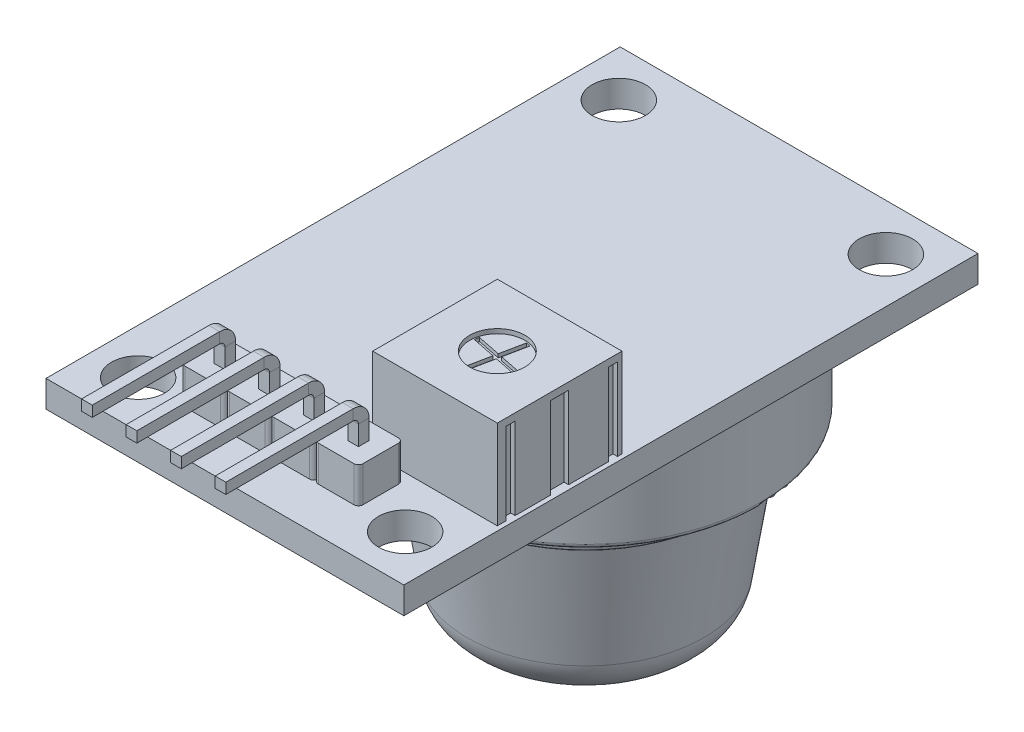
SolidWorks part; units mm, degrees
ref_plane "Front Plane" through (0, 0, 0) normal (0, 0, 1) x (1, 0, 0)
ref_plane "Top Plane" through (0, 0, 0) normal (0, 1, 0) x (1, 0, 0)
ref_plane "Right Plane" through (0, 0, 0) normal (1, 0, 0) x (0, 0, -1)
sketch "Sketch1" plane through (0, 0, 0) normal (0, 1, 0) x (1, 0, 0)
  line L1 (0, 0) -> (20.1, 0)
  line L2 (0, 0) -> (0, -32.25)
  line L3 (0, -32.25) -> (20.1, -32.25)
  line L4 (20.1, 0) -> (20.1, -32.25)
  line L5 (2.55, -2.625) -> (17.55, -2.625) construction
  line L6 (2.55, -2.625) -> (2.55, -29.625) construction
  line L7 (2.55, -29.625) -> (17.55, -29.625) construction
  line L8 (17.55, -2.625) -> (17.55, -29.625) construction
  line L9 (2.55, -2.625) -> (17.55, -29.625) construction
  line L10 (2.55, -29.625) -> (17.55, -2.625) construction
  circle A0 centre (2.55, -2.625) radius 1.5
  circle A1 centre (17.55, -2.625) radius 1.5
  circle A2 centre (2.55, -29.625) radius 1.5
  circle A3 centre (17.55, -29.625) radius 1.5
  point P5 (10.05, -16.125)
  dimension "D5" = 3
  dimension "D1" = 32.25
  dimension "D2" = 20.1
  dimension "D3" = 27
  dimension "D4" = 15
extrude "Boss-Extrude1" add sketch "Sketch1" along normal blind 1.5
sketch "Sketch2" plane through (0, 1.5, 0) normal (0, 1, 0) x (1, 0, 0)
  line L1 (5.3, -27.25) -> (7.3, -27.25)
  line L2 (5.05, -27.5) -> (5.05, -29.5)
  line L3 (5.3, -29.75) -> (7.3, -29.75)
  line L4 (6, -28.2) -> (6.6, -28.2)
  line L5 (7.8, -27.25) -> (9.8, -27.25)
  line L6 (6, -28.2) -> (6, -28.8)
  line L8 (6, -28.8) -> (6.6, -28.8)
  line L9 (7.8, -29.75) -> (9.8, -29.75)
  line L10 (6.6, -28.2) -> (6.6, -28.8)
  line L12 (9.1, -28.2) -> (9.1, -28.8)
  line L13 (8.5, -28.8) -> (9.1, -28.8)
  line L14 (6, -28.2) -> (6.6, -28.8) construction
  line L15 (8.5, -28.2) -> (8.5, -28.8)
  line L16 (8.5, -28.2) -> (9.1, -28.2)
  line L17 (0, 0) -> (0, -32.25) construction
  line L18 (0, -32.25) -> (20.1, -32.25) construction
  line L19 (10.3, -27.25) -> (12.3, -27.25)
  line L21 (10.3, -29.75) -> (12.3, -29.75)
  line L22 (6, -28.8) -> (6.6, -28.2) construction
  line L24 (11.6, -28.2) -> (11.6, -28.8)
  line L25 (11, -28.8) -> (11.6, -28.8)
  line L26 (11, -28.2) -> (11, -28.8)
  line L27 (11, -28.2) -> (11.6, -28.2)
  line L28 (12.8, -27.25) -> (14.8, -27.25)
  line L29 (15.05, -27.5) -> (15.05, -29.5)
  line L30 (12.8, -29.75) -> (14.8, -29.75)
  line L32 (14.1, -28.2) -> (14.1, -28.8)
  line L33 (13.5, -28.8) -> (14.1, -28.8)
  line L34 (13.5, -28.2) -> (13.5, -28.8)
  line L35 (13.5, -28.2) -> (14.1, -28.2)
  line L36 (7.55, -27.5) -> (7.55, -29.5) [skipped]
  line L37 (10.05, -27.5) -> (10.05, -29.5) [skipped]
  line L38 (12.55, -27.5) -> (12.55, -29.5) [skipped]
  arc A0 (7.3, -29.75) -> (7.55, -29.5) centre (7.3, -29.5) ccw
  arc A1 (5.05, -29.5) -> (5.3, -29.75) centre (5.3, -29.5) ccw
  arc A2 (5.05, -27.5) -> (5.3, -27.25) centre (5.3, -27.5) cw
  arc A3 (7.55, -27.5) -> (7.3, -27.25) centre (7.3, -27.5) ccw
  arc A4 (10.05, -27.5) -> (9.8, -27.25) centre (9.8, -27.5) ccw
  arc A5 (9.8, -29.75) -> (10.05, -29.5) centre (9.8, -29.5) ccw
  arc A6 (7.55, -29.5) -> (7.8, -29.75) centre (7.8, -29.5) ccw
  arc A7 (7.55, -27.5) -> (7.8, -27.25) centre (7.8, -27.5) cw
  arc A8 (12.55, -27.5) -> (12.3, -27.25) centre (12.3, -27.5) ccw
  arc A9 (12.3, -29.75) -> (12.55, -29.5) centre (12.3, -29.5) ccw
  arc A10 (10.05, -29.5) -> (10.3, -29.75) centre (10.3, -29.5) ccw
  arc A11 (10.05, -27.5) -> (10.3, -27.25) centre (10.3, -27.5) cw
  arc A12 (15.05, -27.5) -> (14.8, -27.25) centre (14.8, -27.5) ccw
  arc A13 (14.8, -29.75) -> (15.05, -29.5) centre (14.8, -29.5) ccw
  arc A14 (12.55, -29.5) -> (12.8, -29.75) centre (12.8, -29.5) ccw
  arc A15 (12.55, -27.5) -> (12.8, -27.25) centre (12.8, -27.5) cw
  point P8 (5.05, -29.75)
  point P11 (5.05, -27.25)
  point P14 (7.55, -27.25)
  point P23 (6.3, -28.5)
  dimension "D3" = 0.25
  dimension "D1" = 2.5
  dimension "D2" = 2.5
  dimension "D5" = 5.05
  dimension "D6" = 2.5
  dimension "D7" = 0.6
  dimension "D8" = 0.6
extrude "Boss-Extrude2" add sketch "Sketch2" along normal blind 2
sketch "Sketch3" plane through (5.05, 0, 0) normal (-1, 0, 0) x (0, 0, 1)
  line L0 (28.5, -1.2) -> (28.5, 4.6)
  line L2 (29.1, 5.2) -> (36.25, 5.2)
  line L3 (0, 0) -> (32.25, 0) construction
  line L4 (27.25, 3.5) -> (27.25, 1.5) construction
  line L6 (28.5, -1.2) -> (31.7504, -1.2) construction
  arc A0 (29.1, 5.2) -> (28.5, 4.6) centre (29.1, 4.6) ccw
  dimension "D2" = 0.6
  dimension "D1" = 5.2
  dimension "D3" = 9
sketch "Sketch4" plane through (0, 1.5, 0) normal (0, 1, 0) x (1, 0, 0)
  line L0 (8.5, -28.2) -> (9.1, -28.2)
  line L1 (6, -28.2) -> (6.6, -28.2)
  line L2 (6, -28.2) -> (6, -28.8)
  line L3 (6, -28.8) -> (6.6, -28.8)
  line L4 (6.6, -28.2) -> (6.6, -28.8)
  line L5 (6, -28.2) -> (6.6, -28.8) construction
  line L6 (6, -28.8) -> (6.6, -28.2) construction
  line L7 (9.1, -28.2) -> (9.1, -28.8)
  line L8 (8.5, -28.8) -> (9.1, -28.8)
  line L9 (8.5, -28.2) -> (8.5, -28.8)
  line L10 (11, -28.2) -> (11.6, -28.2)
  line L11 (11.6, -28.2) -> (11.6, -28.8)
  line L12 (11, -28.8) -> (11.6, -28.8)
  line L13 (11, -28.2) -> (11, -28.8)
  line L14 (13.5, -28.2) -> (14.1, -28.2)
  line L15 (14.1, -28.2) -> (14.1, -28.8)
  line L16 (13.5, -28.8) -> (14.1, -28.8)
  line L17 (13.5, -28.2) -> (13.5, -28.8)
  point P0 (6.3, -28.5)
  dimension "D1" = 0.6
  dimension "D2" = 0.6
extrude "Cut-Extrude1" cut sketch "Sketch4" against normal up to surface (1.5 mm away) up to face at (10.05, 0, 16.125)
ref_plane "Plane1" through (0, -1.2, 0) normal (0, -1, 0) x (-1, 0, 0)
sketch "Sketch5" plane through (0, -1.2, 0) normal (0, -1, 0) x (-1, 0, 0)
  line L1 (-6, -28.8) -> (-6.6, -28.8)
  line L2 (-6, -28.8) -> (-6, -28.2)
  line L3 (-6, -28.2) -> (-6.6, -28.2)
  line L4 (-6.6, -28.8) -> (-6.6, -28.2)
  line L5 (-8.5, -28.8) -> (-9.1, -28.8)
  line L6 (-8.5, -28.8) -> (-8.5, -28.2)
  line L7 (-8.5, -28.2) -> (-9.1, -28.2)
  line L8 (-9.1, -28.8) -> (-9.1, -28.2)
  line L9 (-11, -28.8) -> (-11.6, -28.8)
  line L10 (-11, -28.8) -> (-11, -28.2)
  line L11 (-11, -28.2) -> (-11.6, -28.2)
  line L12 (-11.6, -28.8) -> (-11.6, -28.2)
  line L13 (-13.5, -28.8) -> (-14.1, -28.8)
  line L14 (-13.5, -28.8) -> (-13.5, -28.2)
  line L15 (-13.5, -28.2) -> (-14.1, -28.2)
  line L16 (-14.1, -28.8) -> (-14.1, -28.2)
sweep "Sweep1" add profiles "Sketch5" path "Sketch3"
sketch "Sketch6" plane through (0, 1.5, 0) normal (0, 1, 0) x (1, 0, 0)
  line L0 (20.1, -32.25) -> (20.1, 0) construction
  line L1 (19.85, -19.75) -> (12.85, -19.75)
  line L2 (19.85, -19.75) -> (19.85, -26.75)
  line L3 (19.85, -26.75) -> (12.85, -26.75)
  line L4 (12.85, -19.75) -> (12.85, -26.75)
  line L5 (0, -32.25) -> (20.1, -32.25) construction
  dimension "D1" = 7
  dimension "D2" = 7
  dimension "D3" = 5.5
  dimension "D4" = 0.25
extrude "Boss-Extrude3" add sketch "Sketch6" along normal blind 5 separate body
sketch "Sketch7" plane through (0, 1.5, 0) normal (0, -1, 0) x (1, 0, 0)
  line L0 (19.85, 26.75) -> (19.85, 19.75) construction
  line L1 (20.1, 23.75) -> (19.6, 23.75)
  line L2 (20.1, 23.75) -> (20.1, 22.75)
  line L3 (20.1, 22.75) -> (19.6, 22.75)
  line L4 (19.6, 23.75) -> (19.6, 22.75)
  line L5 (20.1, 23.75) -> (19.6, 22.75) construction
  line L6 (20.1, 22.75) -> (19.6, 23.75) construction
  line L7 (12.85, 26.75) -> (19.85, 26.75) construction
  line L8 (19.6, 26.25) -> (20.1, 26.25)
  line L9 (19.6, 26.25) -> (19.6, 25.75)
  line L10 (19.6, 25.75) -> (20.1, 25.75)
  line L11 (20.1, 26.25) -> (20.1, 25.75)
  line L12 (19.6, 26.25) -> (20.1, 25.75) construction
  line L13 (19.6, 25.75) -> (20.1, 26.25) construction
  line L14 (19.6, 20.5) -> (20.1, 20.5)
  line L15 (19.6, 20.5) -> (19.6, 20)
  line L16 (19.6, 20) -> (20.1, 20)
  line L17 (20.1, 20.5) -> (20.1, 20)
  line L18 (19.6, 20.5) -> (20.1, 20) construction
  line L19 (19.6, 20) -> (20.1, 20.5) construction
  line L20 (19.85, 19.75) -> (12.85, 19.75) construction
  point P0 (19.85, 23.25)
  point P7 (19.85, 26)
  point P12 (19.85, 20.25)
  dimension "D1" = 0.5
  dimension "D2" = 0.25
  dimension "D3" = 1
  dimension "D4" = 0.5
  dimension "D5" = 0.5
  dimension "D6" = 0.5
  dimension "D7" = 0.5
  dimension "D8" = 0.5
extrude "Cut-Extrude2" cut sketch "Sketch7" against normal blind 4.6
sketch "Sketch8" plane through (0, 6.5, 0) normal (0, 1, 0) x (1, 0, 0)
  circle A0 centre (16.35, -23.25) radius 1.55
  dimension "D1" = 3.1
extrude "Cut-Extrude3" cut sketch "Sketch8" against normal blind 0.25
sketch "Sketch9" plane through (0, 6.25, 0) normal (0, 1, 0) x (1, 0, 0)
  line L0 (16.6442, -21.8071) -> (16.0558, -24.6929) construction
  line L1 (16.5206, -21.7873) -> (16.2525, -23.1025)
  line L2 (16.7656, -21.8373) -> (16.4975, -23.1525)
  line L3 (14.9071, -22.9558) -> (17.7929, -23.5442) construction
  line L4 (14.9373, -22.8344) -> (16.2525, -23.1025)
  line L5 (14.8873, -23.0794) -> (16.2025, -23.3475)
  line L6 (16.2025, -23.3475) -> (15.9344, -24.6627)
  line L7 (16.4975, -23.1525) -> (17.8127, -23.4206)
  line L8 (16.4475, -23.3975) -> (16.1794, -24.7127)
  line L9 (16.4475, -23.3975) -> (17.7627, -23.6656)
  arc A0 (14.9373, -22.8344) -> (14.8873, -23.0794) centre (16.35, -23.25) ccw
  arc A1 (16.7656, -21.8373) -> (16.5206, -21.7873) centre (16.35, -23.25) ccw
  arc A2 (17.7627, -23.6656) -> (17.8127, -23.4206) centre (16.35, -23.25) ccw
  arc A3 (15.9344, -24.6627) -> (16.1794, -24.7127) centre (16.35, -23.25) ccw
  dimension "D1" = 0.125
  dimension "D2" = 0.125
  dimension "D3" = 90
  dimension "D4" = 0.125
  dimension "D5" = 0.125
extrude "Cut-Extrude4" cut sketch "Sketch9" against normal blind 0.2
sketch "Sketch10" plane through (0, 0, 0) normal (0, -1, 0) x (1, 0, 0)
  line L0 (0, 2.2) -> (20.1, 2.2) construction
  line L1 (0, 0) -> (0, 32.25) construction
  line L2 (20.1, 32.25) -> (20.1, 0) construction
  line L3 (20.1, 0) -> (0, 0) construction
  circle A0 centre (10.05, 12) radius 9.8
  dimension "D1" = 19.6
  dimension "D2" = 2.2
ref_plane "Plane2" through (0, 0, 12) normal (0, 0, -1) x (-1, 0, 0)
sketch "Sketch11" plane through (0, 0, 12) normal (0, 0, -1) x (-1, 0, 0)
  line L0 (-10.05, 0) -> (-0.5, 0)
  line L1 (-19.85, 0) -> (-0.25, 0) construction
  line L2 (0, 0) -> (-20.1, 0) construction
  line L3 (-0.25, -0.25) -> (-0.25, -4.75)
  line L4 (-0.5, -5) -> (-1.8382, -5)
  line L5 (-2.0848, -5.2089) -> (-2.293, -6.4582)
  line L6 (-2.3424, -6.5) -> (-2.4, -6.5)
  line L7 (-2.4, -6.5) -> (-3.3931, -12.8843)
  line L8 (-5.8634, -15) -> (-10.05, -15)
  line L9 (-10.05, -15) -> (-10.05, 0)
  arc A0 (-2.0848, -5.2089) -> (-1.8382, -5) centre (-1.8382, -5.25) cw
  arc A1 (-0.5, -5) -> (-0.25, -4.75) centre (-0.5, -4.75) ccw
  arc A2 (-0.25, -0.25) -> (-0.5, 0) centre (-0.5, -0.25) ccw
  arc A4 (-2.3424, -6.5) -> (-2.293, -6.4582) centre (-2.3424, -6.45) ccw
  arc A5 (-5.8634, -15) -> (-3.3931, -12.8843) centre (-5.8634, -12.5) ccw
  point P14 (-2.05, -5)
  point P17 (-0.25, -5)
  point P20 (-0.25, 0)
  point P23 (-2.4, -6.5)
  point P26 (-2.3, -6.5)
  point P29 (-3.8, -15)
  dimension "D8" = 0.25
  dimension "D10" = 2.5
  dimension "D1" = 5
  dimension "D2" = 8
  dimension "D3" = 7.75
  dimension "D4" = 1.5
  dimension "D5" = 0.1
  dimension "D6" = 15
  dimension "D7" = 6.25
revolve "Revolve1" add sketch "Sketch11" angle 360 about L9
